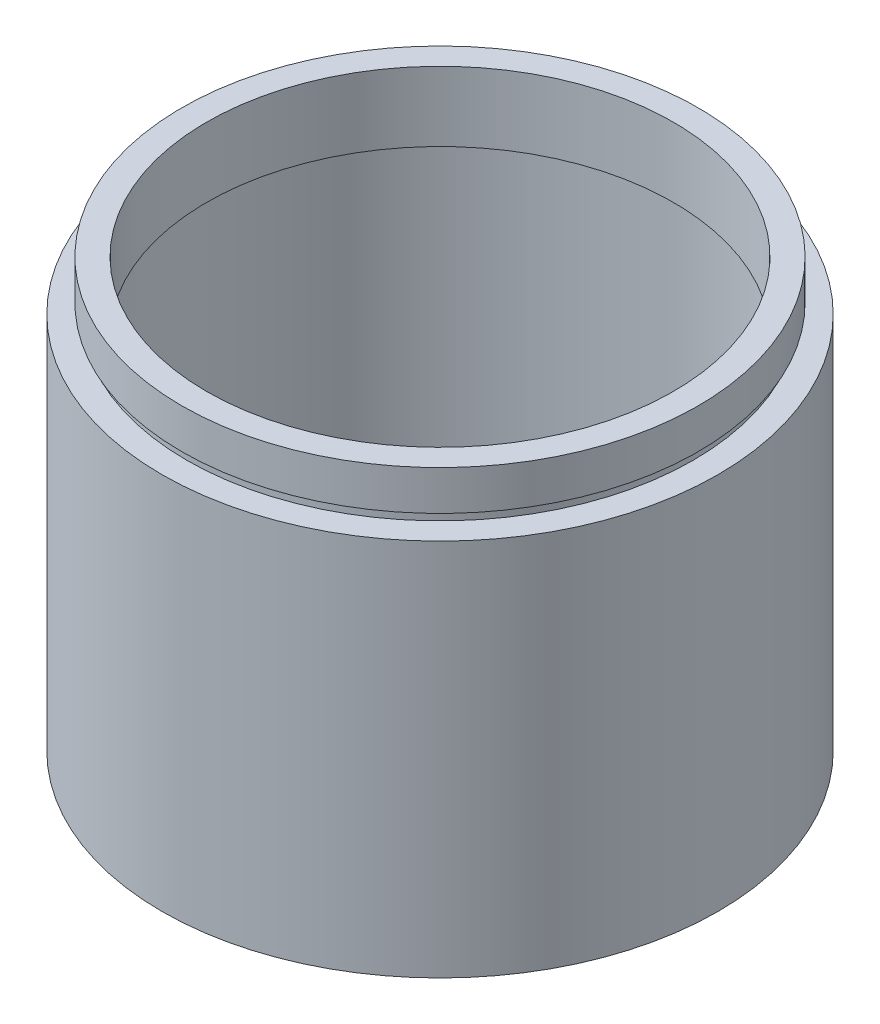
SolidWorks part; units mm, degrees
ref_plane "前视基准面" through (0, 0, 0) normal (0, 0, 1) x (1, 0, 0)
ref_plane "上视基准面" through (0, 0, 0) normal (0, 1, 0) x (1, 0, 0)
ref_plane "右视基准面" through (0, 0, 0) normal (1, 0, 0) x (0, 0, -1)
sketch "草图1" plane through (0, 0, 0) normal (0, 0, 1) x (1, 0, 0)
  line L0 (0, 161.3762) -> (0, 0) construction
  line L1 (141.7365, 0) -> (-131.7984, 0) construction
  line L2 (23.5, 43.1) -> (26, 43.1)
  line L3 (26, 43.1) -> (26, 39.1)
  line L4 (26, 39.1) -> (25.5, 39.1)
  line L5 (25.5, 39.1) -> (25.5, 38.1)
  line L6 (25.5, 38.1) -> (28, 38.1)
  line L7 (28, 38.1) -> (28, 0)
  line L8 (28, 0) -> (25.5, 0)
  line L9 (25.5, 0) -> (25.5, 35.1)
  line L10 (25.5, 35.1) -> (26.1, 35.1)
  line L11 (26.1, 35.1) -> (26.1, 36.1)
  line L12 (26.1, 36.1) -> (23.5, 36.1)
  line L13 (23.5, 36.1) -> (23.5, 43.1)
  dimension "D1" = 23.5
  dimension "D2" = 26
  dimension "D3" = 1
  dimension "D4" = 1
  dimension "D5" = 25.5
  dimension "D6" = 26.1
  dimension "D7" = 25.5
  dimension "D8" = 5
  dimension "D9" = 7
  dimension "D10" = 38.1
  dimension "D11" = 28
revolve "旋转1" add sketch "草图1" angle 360 about L0
cosmetic thread "装饰螺纹线1" parameters "D2"=52
cosmetic thread "装饰螺纹线2" parameters "D2"=48
cosmetic thread "装饰螺纹线3" parameters "D2"=51
